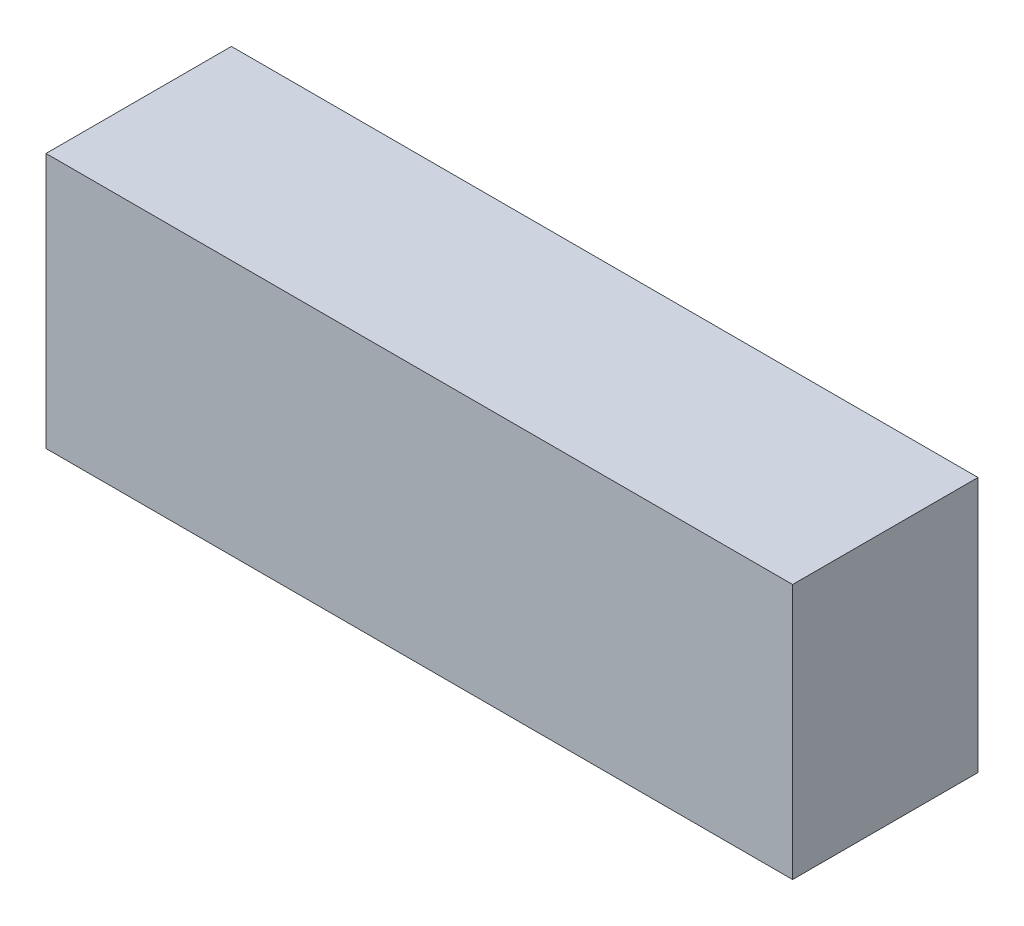
SolidWorks part; units mm, degrees
ref_plane "Front Plane" through (0, 0, 0) normal (0, 0, 1) x (1, 0, 0)
ref_plane "Top Plane" through (0, 0, 0) normal (0, 1, 0) x (1, 0, 0)
ref_plane "Right Plane" through (0, 0, 0) normal (1, 0, 0) x (0, 0, -1)
sketch "Sketch1" plane through (0, 0, 0) normal (0, 1, 0) x (1, 0, 0)
  line L1 (0, 0) -> (149, 0)
  line L2 (0, 0) -> (0, 37)
  line L3 (0, 37) -> (149, 37)
  line L4 (149, 0) -> (149, 37)
  dimension "D1" = 149
  dimension "D2" = 37
extrude "Boss-Extrude1" add sketch "Sketch1" along normal blind 51
